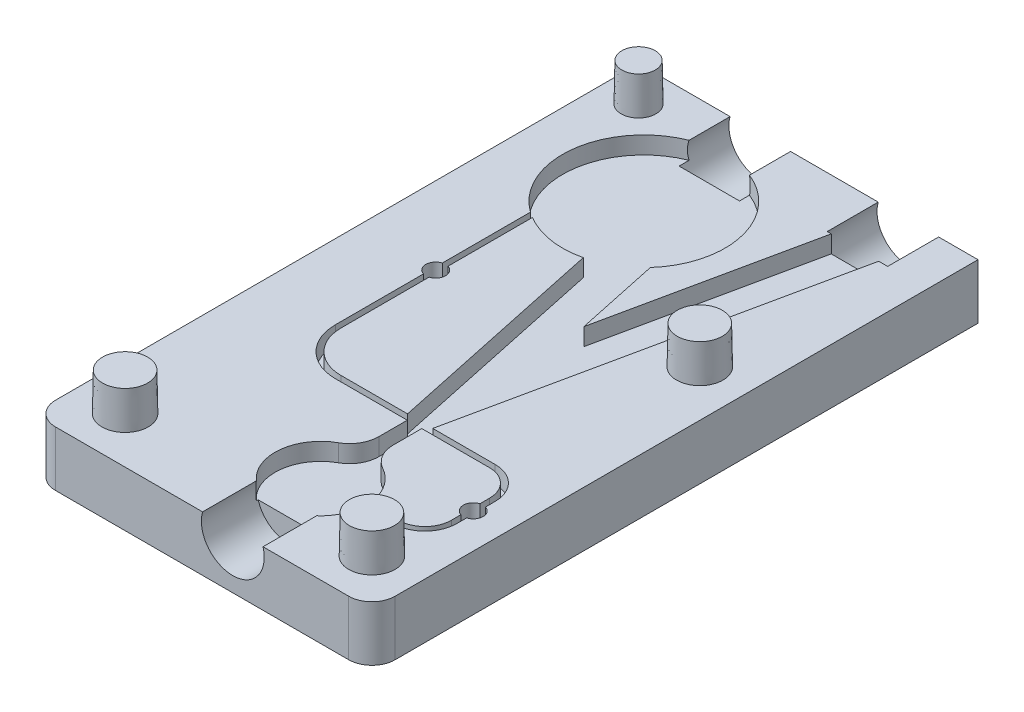
SolidWorks part; units mm, degrees
material "ABS"
ref_plane "Front Plane" through (0, 0, 0) normal (0, 0, 1) x (1, 0, 0)
ref_plane "Top Plane" through (0, 0, 0) normal (0, 1, 0) x (1, 0, 0)
ref_plane "Right Plane" through (0, 0, 0) normal (1, 0, 0) x (0, 0, -1)
sketch "Sketch1" plane through (0, 0, 0) normal (0, 1, 0) x (1, 0, 0)
  line L1 (-23.25, 41.5) -> (23.25, 41.5)
  line L2 (-23.25, 41.5) -> (-23.25, -41.5)
  line L3 (-23.25, -41.5) -> (23.25, -41.5)
  line L4 (23.25, 41.5) -> (23.25, -41.5)
  line L5 (-23.25, 41.5) -> (23.25, -41.5) construction
  line L6 (-23.25, -41.5) -> (23.25, 41.5) construction
  point P0 (0, 0)
  dimension "D1" = 46.5
  dimension "D2" = 83
extrude "Boss-Extrude1" add sketch "Sketch1" along normal blind 7.5406
sketch "Sketch2" plane through (0, 0, 0) normal (0, 1, 0) x (1, 0, 0)
  line L1 (-12.65, -10.23) -> (-12.65, 25.55) construction
  line L11 (9.4726, 31.3805) -> (10.4806, 36.123)
  line L17 (10.55, 36.7831) -> (10.55, 41.5)
  line L22 (-23.25, -41.5) -> (23.25, -41.5) construction
  line L23 (0.7075, -41.5) -> (7.6925, -41.5)
  line L24 (0.7075, -41.5) -> (0.7075, -34.6481)
  line L25 (9.4726, 31.3805) -> (4.2, 6.575)
  line L26 (15.6838, 30.0603) -> (16.6919, 34.8027)
  line L27 (4.2, 6.575) -> (0.1667, 25.55)
  line L28 (16.9, 36.7831) -> (16.9, 41.5)
  line L29 (0.1667, 25.55) -> (-6.0445, 24.2298)
  line L30 (-6.0445, 24.2298) -> (2.4737, -15.845)
  line L31 (-6.65, -16.23) -> (14.4748, -16.23) construction
  line L32 (3.2078, -16.615) -> (3.2078, -23.2943)
  line L33 (5.1922, -23.2943) -> (5.1922, -16.615)
  line L34 (4.2, 6.575) -> (4.2, 41.5) construction
  line L35 (18.4748, -20.23) -> (18.4748, -25.465) construction
  line L36 (14.4748, -29.465) -> (4.2, -29.465) construction
  line L37 (0.7075, -34.6481) -> (7.6925, -34.6481)
  line L38 (7.6925, -41.5) -> (7.6925, -34.6481)
  line L39 (15.6838, 30.0603) -> (5.9263, -15.845)
  line L40 (23.25, 41.5) -> (-23.25, 41.5) construction
  line L41 (4.2, 6.575) -> (10.6919, 6.575) construction
  line L42 (23.25, -41.5) -> (23.25, 41.5) construction
  line L43 (-23.25, 41.5) -> (-23.25, -41.5) construction
  line L44 (14.4748, -29.85) -> (4.2, -29.85)
  line L45 (18.8598, -20.23) -> (18.8598, -25.465)
  line L46 (-6.65, -15.845) -> (14.4748, -15.845)
  line L47 (-12.265, -10.23) -> (-12.265, 25.55)
  line L48 (14.4748, -29.08) -> (4.2, -29.08)
  line L49 (18.0898, -20.23) -> (18.0898, -25.465)
  line L50 (-6.65, -16.615) -> (14.4748, -16.615)
  line L51 (-13.035, -10.23) -> (-13.035, 25.55)
  line L52 (9.4726, 31.3805) -> (15.6838, 30.0603) construction
  line L53 (3.2078, -19.9546) -> (5.1922, -19.9546) construction
  line L54 (4.2, -19.9546) -> (4.2, -29.465) construction
  line L55 (10.55, 41.5) -> (16.9, 41.5)
  circle A6 centre (-6.56, 25.55) radius 11.13
  arc A7 (14.4748, -16.23) -> (18.4748, -20.23) centre (14.4748, -20.23) cw construction
  arc A8 (18.4748, -25.465) -> (14.4748, -29.465) centre (14.4748, -25.465) cw construction
  circle A9 centre (4.2, -29.465) radius 6.25
  arc A11 (-12.65, -10.23) -> (-6.65, -16.23) centre (-6.65, -10.23) ccw construction
  arc A12 (18.8598, -25.465) -> (14.4748, -29.85) centre (14.4748, -25.465) cw
  arc A13 (14.4748, -15.845) -> (18.8598, -20.23) centre (14.4748, -20.23) cw
  arc A14 (-12.265, -10.23) -> (-6.65, -15.845) centre (-6.65, -10.23) ccw
  arc A15 (18.0898, -25.465) -> (14.4748, -29.08) centre (14.4748, -25.465) cw
  arc A16 (14.4748, -16.615) -> (18.0898, -20.23) centre (14.4748, -20.23) cw
  arc A17 (-13.035, -10.23) -> (-6.65, -16.615) centre (-6.65, -10.23) ccw
  arc A18 (5.1922, -20.5129) -> (7.244, -24.0064) centre (9.1922, -20.5129) ccw
  arc A19 (1.156, -24.0064) -> (3.2078, -20.5129) centre (-0.7922, -20.5129) ccw
  circle A20 centre (-6.56, 25.55) radius 7.95 construction
  circle A21 centre (-6.56, 25.55) radius 9.525 construction
  arc A22 (10.4806, 36.123) -> (10.55, 36.7831) centre (7.375, 36.7831) ccw
  arc A23 (16.6919, 34.8027) -> (16.9, 36.7831) centre (7.375, 36.7831) ccw
  point P80 (13.725, 41.5)
  dimension "D18" = 14.2748
  dimension "D19" = 3.4527
  dimension "D20" = 19.05
  dimension "D25" = 9.525
  dimension "D26" = 9.525
  dimension "D16" = 6.985
  dimension "D13" = 6
  dimension "D6" = 22.26
  dimension "D14" = 12.5
  dimension "D17" = 4
  dimension "D22" = 4
  dimension "D23" = 15.9
  dimension "D24" = 19.05
  dimension "D1" = 34.925
  dimension "D2" = 12.5581
  dimension "D3" = 12
  dimension "D4" = 1.9844
  dimension "D5" = 16.69
  dimension "D7" = 10.6
  dimension "D8" = 15.95
  dimension "D9" = 6.35
  dimension "D10" = 0.385
  dimension "D11" = 0.385
  dimension "D12" = 25.27
  dimension "D15" = 12.85
  dimension "D21" = 6.35
extrude "Cut-Extrude3" cut sketch "Sketch2" against normal blind 2.3813 from surface at 7.5406
hole_wizard "1/4 NPT Tapped Hole1" [suppressed] positions "Sketch4" profile "Sketch6" size "1/4" standard "ANSI Inch"
sketch "Sketch4" plane through (0, 0, 41.5) normal (0, 0, 1) x (1, 0, 0)
  line L2 (4.2, -3.9624) -> (4.2, 3.9688) construction
  line L3 (9.2, 3.9688) -> (-0.8, 3.9688) construction
  line L4 (9.2, 6.35) -> (23.25, 6.35) construction
  point P2 (4.2, -3.9624)
  dimension "D1" = 10.3124
sketch "Sketch6" plane through (4.2, -3.9624, 41.5) normal (1, 0, 0) x (0, -1, 0)
  line L0 (0, 0) -> (0, 17.6298)
  line L1 (5.5626, 14.2875) -> (0, 17.6298)
  line L2 (-5.5626, 14.2875) -> (0, 17.6298) construction
  line L3 (5.5626, 14.2875) -> (5.5626, 10.033)
  line L4 (5.5626, 10.033) -> (6.558, 10.033)
  line L5 (6.558, 10.033) -> (6.8584, 0)
  line L6 (-6.558, 10.033) -> (-6.8584, 0) construction
  line L7 (6.8584, 0) -> (0, 0)
  line L8 (0, -6.35) -> (0, 107.95) construction
  line L11 (-5.5626, 10.033) -> (-6.558, 10.033) construction
  dimension "Tap Drill Dia." = 11.1252
  dimension "Tap Drill Depth" = 14.2875
  dimension "Thread Dia." = 13.7168
  dimension "Thread Angle" = 3.43
  dimension "Thread Depth" = 10.033
  dimension "Drill Angle" = 118
sketch "Sketch7" plane through (0, 7.5406, 0) normal (0, 1, 0) x (1, 0, 0)
  circle A9 centre (4.2, -29.465) radius 6.25
  arc A10 (1.156, -24.0064) -> (0.7075, -34.6481) centre (4.2, -29.465) ccw construction
extrude "Cut-Extrude4" [suppressed] cut sketch "Sketch7" against normal blind 10.3124
sketch "Sketch8" plane through (0, 5.1594, 0) normal (0, 1, 0) x (1, 0, 0)
  circle A3 centre (-6.56, 25.55) radius 11.13
  arc A5 (1.7424, 18.1373) -> (-13.035, 16.4973) centre (-6.56, 25.55) ccw construction
extrude "Cut-Extrude5" [suppressed] cut sketch "Sketch8" against normal through all
sketch "Sketch10" plane through (0, 7.5406, 0) normal (0, 1, 0) x (1, 0, 0)
  line L0 (-13.035, 3.1337) -> (-12.265, 3.1337) construction
  line L1 (-13.035, 16.4973) -> (-13.035, -10.23) construction
  line L2 (-12.265, 15.9933) -> (-12.265, -10.23) construction
  line L3 (18.0898, -22.8475) -> (18.8598, -22.8475) construction
  line L4 (18.0898, -25.465) -> (18.0898, -20.23) construction
  line L5 (18.8598, -25.465) -> (18.8598, -20.23) construction
  circle A0 centre (18.4748, -22.8475) radius 1.3525
  circle A1 centre (-12.65, 3.1337) radius 1.3526
  dimension "D1" = 2.7051
  dimension "D2" = 2.7051
extrude "Cut-Extrude6" cut sketch "Sketch10" against normal offset from surface (4.7689 mm away) 2.3876 up to face at (11.8583, 5.1594, 22.6844)
sketch "Sketch11" plane through (0, 7.5406, 0) normal (0, 1, 0) x (1, 0, 0)
  line L0 (10.55, 41.5) -> (-23.25, 41.5) construction
  line L1 (-10.0525, 41.5) -> (-3.0675, 41.5)
  line L2 (-10.0525, 41.5) -> (-10.0525, 36.1178)
  line L3 (-10.0525, 36.1178) -> (-3.0675, 36.1178)
  line L4 (-3.0675, 41.5) -> (-3.0675, 36.1178)
  line L5 (7.6925, -41.5) -> (0.7075, -41.5) construction
  arc A0 (1.7424, 18.1373) -> (-13.035, 16.4973) centre (-6.56, 25.55) ccw construction
  arc A1 (1.7424, 18.1373) -> (-13.035, 16.4973) centre (-6.56, 25.55) ccw construction
extrude "Cut-Extrude7" cut sketch "Sketch11" against normal up to surface (2.3813 mm away) up to face at (5.4073, 5.1594, 8.1039)
sketch "Sketch12" plane through (0, 7.5406, 0) normal (0, 1, 0) x (1, 0, 0)
  line L0 (-23.25, 41.5) -> (-23.25, -41.5) construction
  line L1 (-10.0525, 41.5) -> (-23.25, 41.5) construction
  line L2 (-23.25, -41.5) -> (0.7075, -41.5) construction
  line L3 (7.6925, -41.5) -> (23.25, -41.5) construction
  line L4 (23.25, -41.5) -> (23.25, 41.5) construction
  line L5 (23.25, 41.5) -> (16.9, 41.5) construction
  circle A0 centre (-16.9, -35.15) radius 3.175
  circle A1 centre (16.9, -35.15) radius 3.175
  circle A2 centre (16.9, 9.75) radius 3.175
  circle A3 centre (-18.4748, 36.7375) radius 2.3813
  dimension "D1" = 4.7625
  dimension "D2" = 6.35
  dimension "D3" = 6.35
  dimension "D4" = 6.35
  dimension "D5" = 4.7752
  dimension "D6" = 4.7625
  dimension "D7" = 6.35
  dimension "D8" = 6.35
  dimension "D9" = 6.35
  dimension "D10" = 6.35
  dimension "D11" = 6.35
  dimension "D12" = 31.75
extrude "Boss-Extrude2" add sketch "Sketch12" along normal blind 5.1594 draft 1
fillet "Fillet1" radius 3.175 3 edges at (-23.25, 3.7703, -41.5) (-23.25, 3.7703, 41.5) (23.25, 3.7703, 41.5)
sketch "Sketch13" plane through (0, 0, -41.5) normal (0, 0, -1) x (-1, 0, 0)
  line L0 (-16.9, 6.35) -> (-10.55, 6.35) construction
  line L3 (3.0675, 6.35) -> (10.0525, 6.35) construction
  line L6 (-10.55, 5.1594) -> (-10.55, 7.5406) construction
  line L7 (-16.9, 5.1594) -> (-16.9, 7.5406) construction
  line L8 (10.0525, 5.1594) -> (10.0525, 7.5406) construction
  line L9 (3.0675, 5.1594) -> (3.0675, 7.5406) construction
  circle A0 centre (-13.725, 6.35) radius 4.3053
  circle A1 centre (6.56, 6.35) radius 4.3053
  point P2 (-10.55, 6.35)
  point P3 (-16.9, 6.35)
  point P4 (1.703, 5.1594)
  point P5 (1.56, 6.35)
  point P8 (11.56, 6.35)
  point P9 (-10.55, 6.35)
  point P16 (-16.9, 6.35)
  point P23 (10.1852, 7.5406)
  point P24 (11.56, 6.35)
  point P27 (1.56, 6.35)
  dimension "D1" = 8.6106
  dimension "D2" = 8.6106
extrude "Cut-Extrude8" cut sketch "Sketch13" against normal blind 6.985
sketch "Sketch14" plane through (0, 0, 41.5) normal (0, 0, 1) x (1, 0, 0)
  line L0 (0.7075, 6.35) -> (7.6925, 6.35) construction
  line L1 (7.6925, 5.1594) -> (7.6925, 7.5406) construction
  line L2 (0.7075, 5.1594) -> (0.7075, 7.5406) construction
  circle A0 centre (4.2, 6.35) radius 4.3053
  arc A1 (9.5876, 7.5406) -> (17.8624, 7.5406) centre (13.725, 6.35) ccw construction
  point P9 (9.2, 6.35)
  point P12 (-0.8, 6.35)
extrude "Cut-Extrude9" cut sketch "Sketch14" against normal blind 7.62
